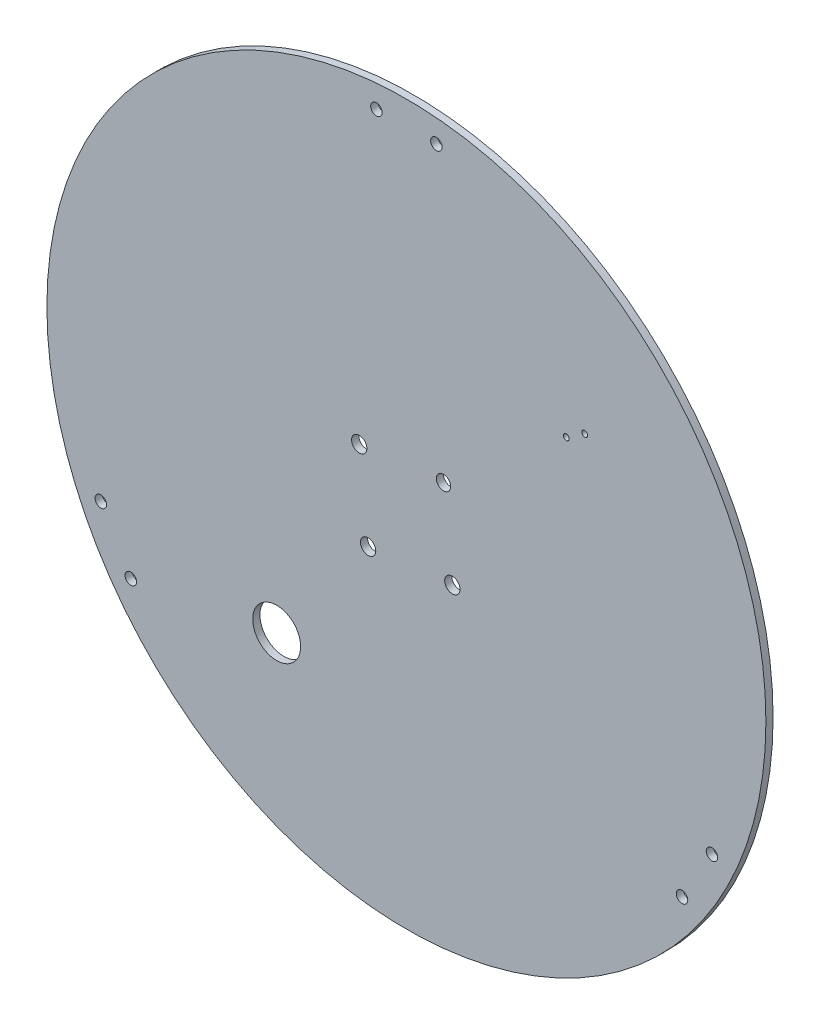
SolidWorks part; units mm, degrees
material "Acrylic (Medium-high impact)"
ref_plane "Front Plane" through (0, 0, 0) normal (0, 0, 1) x (1, 0, 0)
ref_plane "Top Plane" through (0, 0, 0) normal (0, 1, 0) x (1, 0, 0)
ref_plane "Right Plane" through (0, 0, 0) normal (1, 0, 0) x (0, 0, -1)
sketch "Sketch1" plane through (0, 0, 0) normal (0, 0, 1) x (1, 0, 0)
  line L0 (1.0052, 1.2835) -> (1.0052, 141.2835) construction
  line L1 (1.0052, 141.2835) -> (1.0052, 151.2835) construction
  line L2 (-11.4948, 141.2835) -> (13.5052, 141.2835) construction
  line L3 (1.0052, 1.2835) -> (-18.6748, 16.6956) construction
  line L4 (1.0052, 1.2835) -> (1.0052, 232.6259) construction
  line L5 (-18.6748, 16.6956) -> (-168.5906, 134.1006) construction
  line L6 (-138.9884, -36.2405) -> (-113.9884, -79.5418) construction
  line L7 (1.0052, 1.2835) -> (-120.2384, -68.7165) construction
  circle A0 centre (1.0052, 1.2835) radius 150
  circle A1 centre (13.5052, 141.2835) radius 2.4
  circle A2 centre (-11.4948, 141.2835) radius 2.4
  circle A3 centre (128.4987, -57.8912) radius 2.4
  circle A4 centre (115.9987, -79.5418) radius 2.4
  circle A5 centre (-113.9884, -79.5418) radius 2.4
  circle A6 centre (-126.4884, -57.8912) radius 2.4
  circle A10 centre (75.412, 67.4988) radius 1.2
  circle A11 centre (67.712, 62.3988) radius 1.2
  circle A15 centre (20.1825, -14.7704) radius 3.2 construction
  circle A16 centre (-14.9791, -18.466) radius 3.2 construction
  circle A17 centre (16.4869, 20.3913) radius 2.9853 construction
  circle A18 centre (-18.6748, 16.6956) radius 3.2 construction
  circle A19 centre (20.1825, -14.7704) radius 3.2
  circle A20 centre (-14.9791, -18.466) radius 3.2
  circle A21 centre (16.4869, 20.3913) radius 2.9853
  circle A22 centre (-18.6748, 16.6956) radius 3.2
  circle A26 centre (-53.1206, -68.7165) radius 10
  point P9 (1.0052, 141.2835)
  point P12 (-126.4884, -57.8912)
  point P21 (1.0052, 1.2835)
  point P37 (-3.5162, 0.3696)
  dimension "D1" = 300
  dimension "D2" = 3
  dimension "D4" = 4.8
  dimension "D6" = 20
  dimension "D7" = 2.4
  dimension "D8" = 2.4
  dimension "D9" = 51.934
  dimension "D3" = 25
  dimension "D5" = 140
extrude "Boss-Extrude2" add sketch "Sketch1" along normal blind 3
